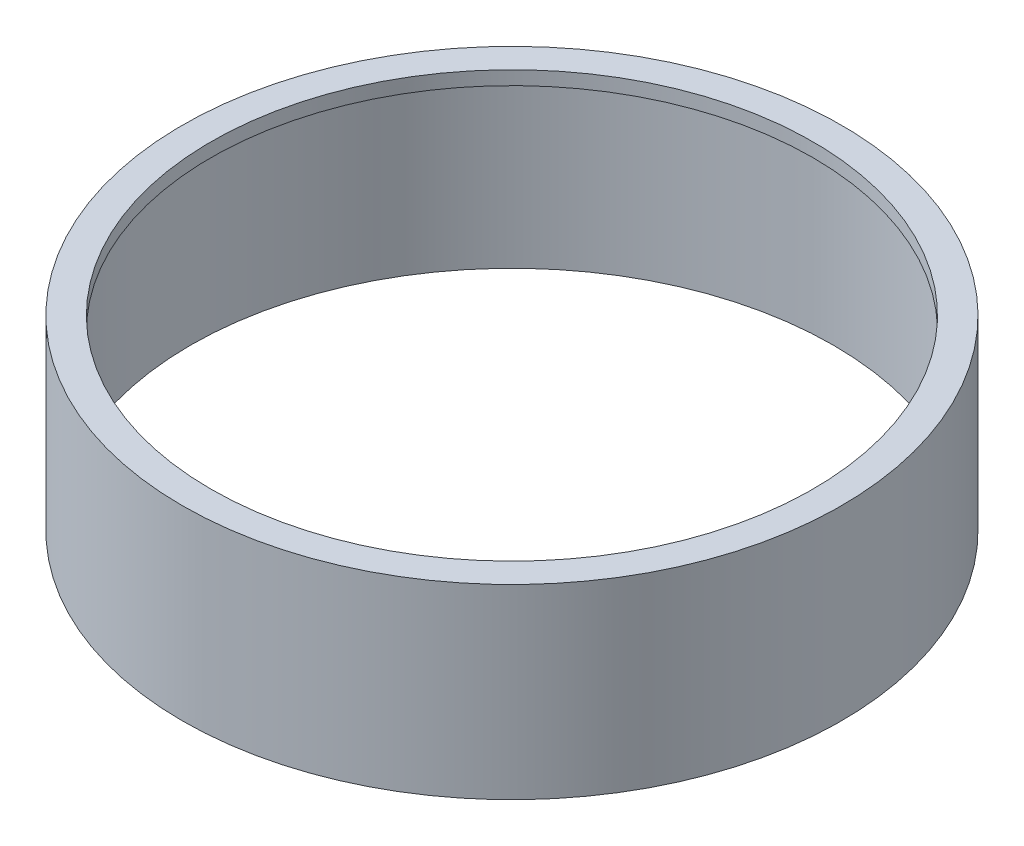
SolidWorks part; units mm, degrees
ref_plane "Front Plane" through (0, 0, 0) normal (0, 0, 1) x (1, 0, 0)
ref_plane "Top Plane" through (0, 0, 0) normal (0, 1, 0) x (1, 0, 0)
ref_plane "Right Plane" through (0, 0, 0) normal (1, 0, 0) x (0, 0, -1)
sketch "Sketch1" plane through (0, 0, 0) normal (0, 1, 0) x (1, 0, 0)
  circle A0 centre (0, 0) radius 40
  dimension "D1" = 80
extrude "Boss-Extrude1" add sketch "Sketch1" along normal blind 22.62 contours A0
sketch "Sketch3" plane through (0, 0, 0) normal (0, -1, 0) x (-1, 0, 0)
  circle A0 centre (0, 0) radius 39
  dimension "D1" = 78
extrude "Cut-Extrude1" cut sketch "Sketch3" against normal blind 20.95
sketch "Sketch4" plane through (0, 22.62, 0) normal (0, 1, 0) x (1, 0, 0)
  circle A0 centre (0, 0) radius 36.525
  dimension "D1" = 73.05
extrude "Cut-Extrude2" cut sketch "Sketch4" against normal through all
equation "\"ODia\"= 3.15in"
equation "\"IDia\"= 3in"
equation "\"InnerLength\"= 20.95mm"
equation "\"OutterLength\"= 22.62mm"
equation "\"LIpDia\"= 73.05mm"
